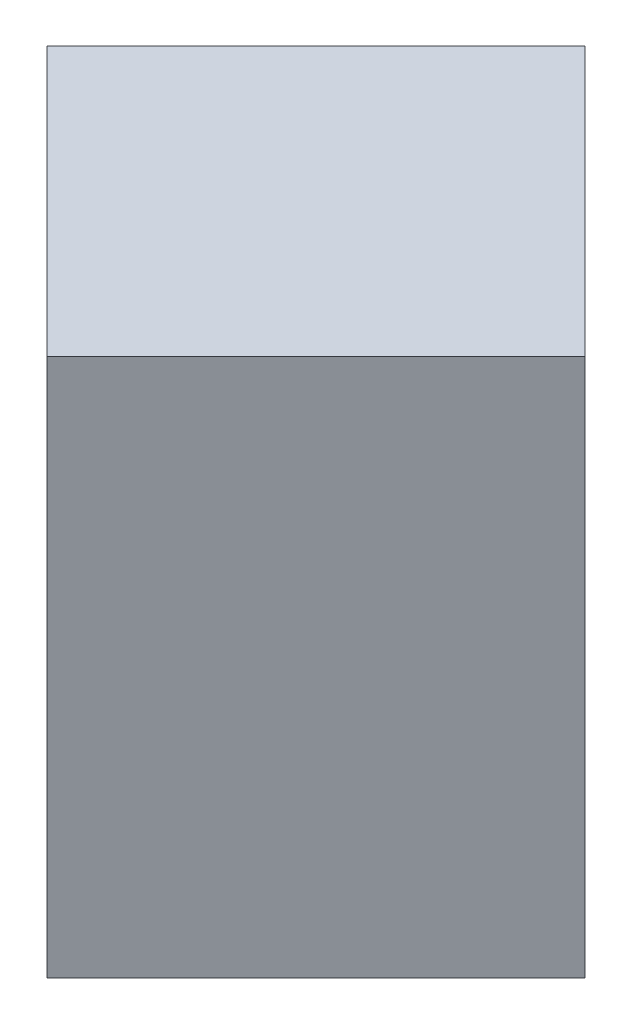
SolidWorks part; units mm, degrees
ref_plane "Front Plane" through (0, 0, 0) normal (0, 0, 1) x (1, 0, 0)
ref_plane "Top Plane" through (0, 0, 0) normal (0, 1, 0) x (1, 0, 0)
ref_plane "Right Plane" through (0, 0, 0) normal (1, 0, 0) x (0, 0, -1)
sketch "Sketch1" plane through (0, 0, 0) normal (0, 0, 1) x (1, 0, 0)
  line L1 (0, 0) -> (20, 0)
  line L2 (0, 0) -> (0, 20)
  line L3 (0, 20) -> (20, 20)
  line L4 (20, 0) -> (20, 20)
  dimension "D1" = 20
  dimension "D2" = 20
extrude "Boss-Extrude1" add sketch "Sketch1" along normal blind 20
sketch "Sketch2" plane through (0, 20, 0) normal (0, 1, 0) x (1, 0, 0)
  line L0 (20, 0) -> (10, 0)
  line L1 (20, 0) -> (0, 0) construction
  line L2 (10, 0) -> (20, -10)
  line L3 (20, -20) -> (20, 0) construction
  line L4 (20, -10) -> (20, 0)
extrude "Cut-Extrude1" cut sketch "Sketch2" against normal blind 20
sketch "Sketch3" plane through (0, 20, 0) normal (0, 1, 0) x (1, 0, 0)
  line L0 (20, -20) -> (20, -10)
  line L1 (20, -10) -> (10, -20)
  line L2 (20, -20) -> (0, -20) construction
  line L3 (10, -20) -> (20, -20)
extrude "Cut-Extrude2" cut sketch "Sketch3" against normal blind 20
sketch "Sketch4" plane through (0, 20, 0) normal (0, 1, 0) x (1, 0, 0)
  line L0 (0, 0) -> (10, 0)
  line L1 (10, 0) -> (0, -10)
  line L2 (0, -20) -> (0, 0) construction
  line L3 (0, -10) -> (0, 0)
extrude "Cut-Extrude3" cut sketch "Sketch4" against normal blind 20
sketch "Sketch5" plane through (0, 20, 0) normal (0, 1, 0) x (1, 0, 0)
  line L0 (0, -20) -> (0, -10)
  line L1 (0, -10) -> (10, -20)
  line L2 (10, -20) -> (0, -20)
extrude "Cut-Extrude4" cut sketch "Sketch5" against normal blind 20
